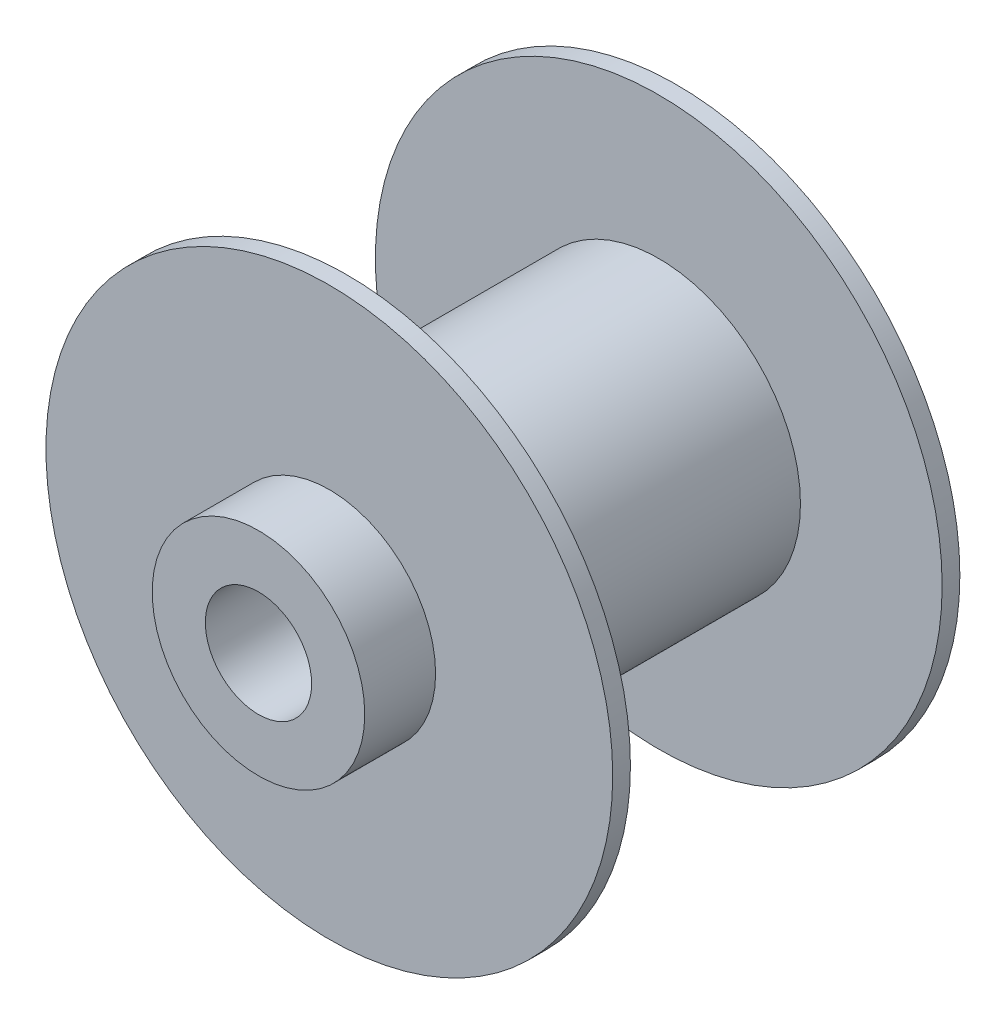
SolidWorks part; units mm, degrees
ref_plane "Front Plane" through (0, 0, 0) normal (0, 0, 1) x (1, 0, 0)
ref_plane "Top Plane" through (0, 0, 0) normal (0, 1, 0) x (1, 0, 0)
ref_plane "Right Plane" through (0, 0, 0) normal (1, 0, 0) x (0, 0, -1)
sketch "Sketch1" plane through (0, 0, 0) normal (0, 0, 1) x (1, 0, 0)
  circle A1 centre (0, 0) radius 50.8
  dimension "D1" = 101.6
extrude "Boss-Extrude1" add sketch "Sketch1" along normal blind 3.175
sketch "Sketch3" plane through (0, 0, 0) normal (0, 0, 1) x (1, 0, 0)
  circle A0 centre (0, 0) radius 25.4
extrude "Boss-Extrude2" add sketch "Sketch3" along normal blind 59.055
sketch "Sketch4" plane through (0, 0, 59.055) normal (0, 0, 1) x (1, 0, 0)
  circle A0 centre (0, 0) radius 50.8
extrude "Boss-Extrude3" add sketch "Sketch4" along normal blind 3.175
sketch "Sketch5" plane through (0, 0, 62.23) normal (0, 0, 1) x (1, 0, 0)
  circle A0 centre (0, 0) radius 19.05
extrude "Boss-Extrude4" add sketch "Sketch5" along normal blind 12.7
sketch "Sketch6" plane through (0, 0, 0) normal (0, 0, -1) x (-1, 0, 0)
  circle A0 centre (0, 0) radius 19.05
extrude "Boss-Extrude5" add sketch "Sketch6" along normal blind 12.7
sketch "Sketch7" plane through (0, 0, 74.93) normal (0, 0, 1) x (1, 0, 0)
  circle A0 centre (0, 0) radius 9.525
extrude "Cut-Extrude1" cut sketch "Sketch7" against normal through all
ref_plane "Plano1" through (0, 0, 31.115) normal (0, 0, 1) x (1, 0, 0)
ref_plane "Plano2" through (0, 0, 31.115) normal (0, 0, 1) x (1, 0, 0)
